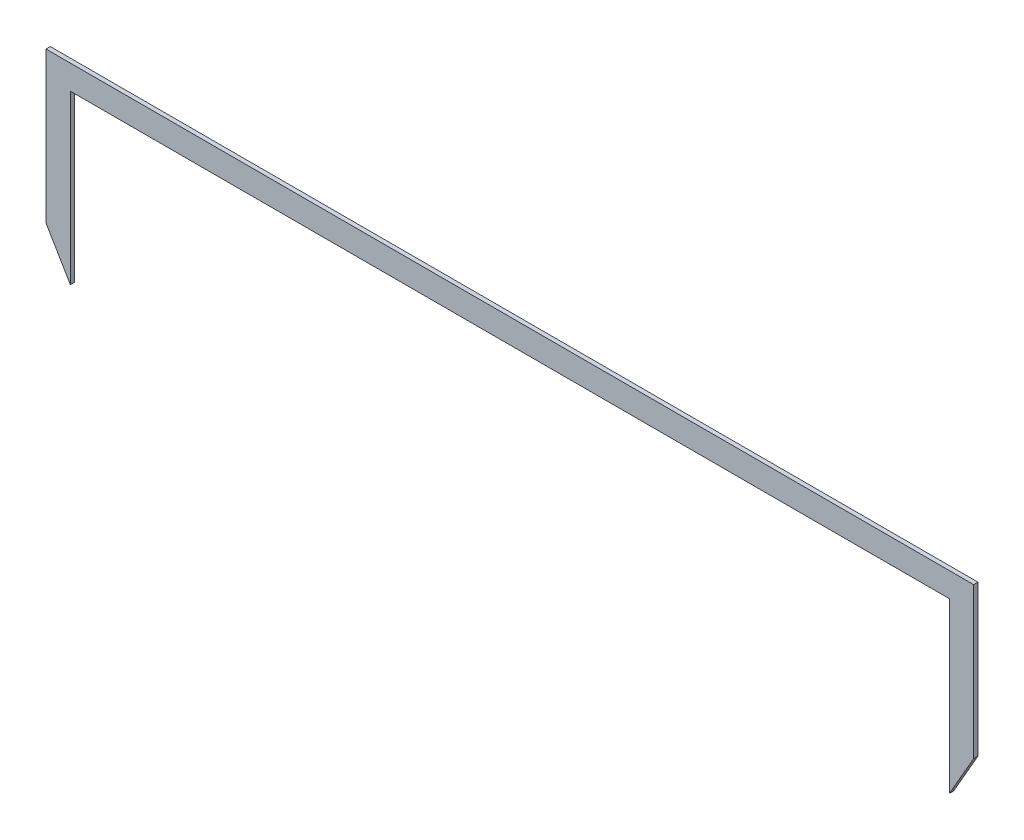
SolidWorks part; units mm, degrees
ref_plane "Front Plane" through (0, 0, 0) normal (0, 0, 1) x (1, 0, 0)
ref_plane "Top Plane" through (0, 0, 0) normal (0, 1, 0) x (1, 0, 0)
ref_plane "Right Plane" through (0, 0, 0) normal (1, 0, 0) x (0, 0, -1)
sketch "Sketch2" plane through (0, 0, 0) normal (0, 0, 1) x (1, 0, 0)
  line L0 (-861.4682, 500.6069) -> (-213.4678, 500.6069)
  line L2 (-213.4678, 395.3747) -> (-213.4678, 500.6069)
  line L4 (-213.4678, 395.3747) -> (-230.4665, 365.7867)
  line L6 (-230.4665, 365.7867) -> (-230.4665, 483.6082)
  line L8 (-230.4665, 483.6082) -> (-844.4695, 483.6082)
  line L10 (-844.4695, 483.6082) -> (-844.4695, 366.5427)
  line L11 (-844.4695, 366.5427) -> (-861.4682, 395.3747)
  line L12 (-861.4682, 395.3747) -> (-861.4682, 500.6069)
extrude "Boss-Extrude1" add sketch "Sketch2" along normal blind 3
